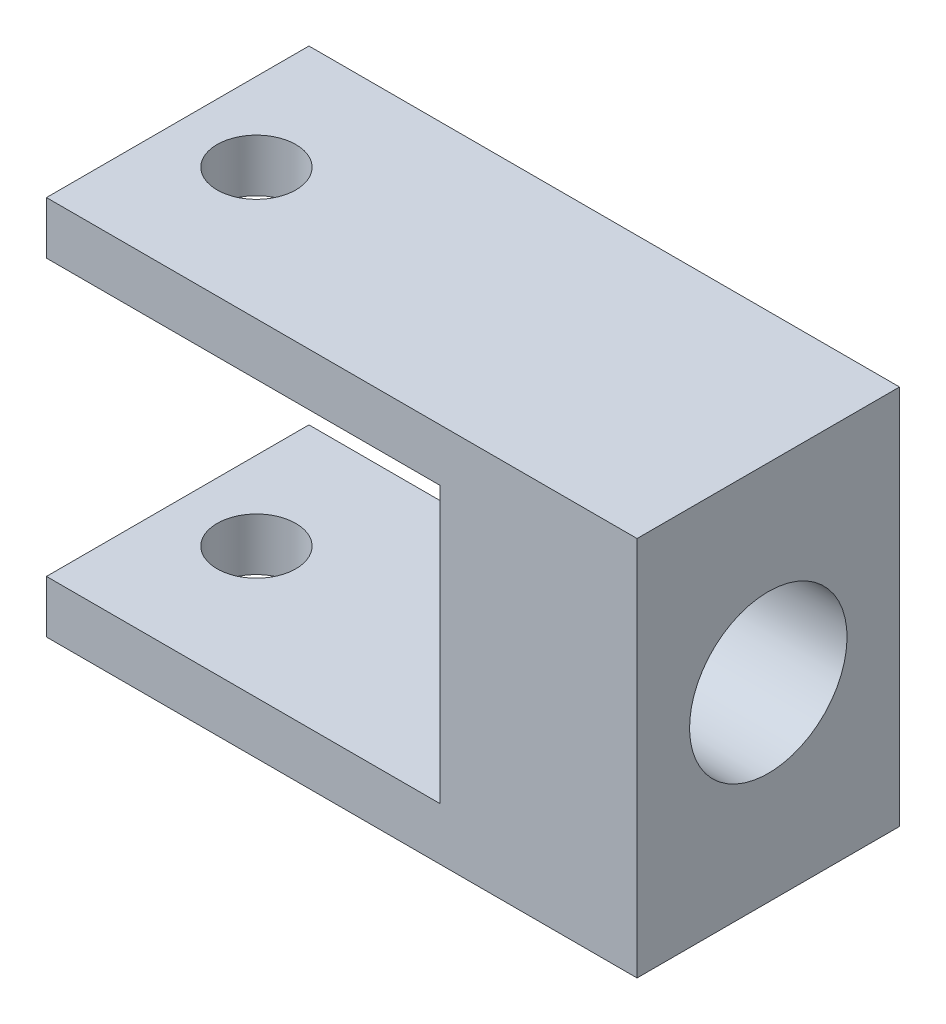
SolidWorks part; units mm, degrees
ref_plane "Ön Düzlem" through (0, 0, 0) normal (0, 0, 1) x (1, 0, 0)
ref_plane "Üst Düzlem" through (0, 0, 0) normal (0, 1, 0) x (1, 0, 0)
ref_plane "Sağ Düzlem" through (0, 0, 0) normal (1, 0, 0) x (0, 0, -1)
sketch "Çizim1" plane through (0, 0, 0) normal (0, 0, 1) x (1, 0, 0)
  line L0 (-22.5, 14.5) -> (22.5, -14.5) construction
  line L1 (-22.5, 14.5) -> (22.5, 14.5)
  line L2 (-22.5, 14.5) -> (-22.5, 10.5)
  line L3 (-22.5, -14.5) -> (22.5, -14.5)
  line L4 (22.5, 14.5) -> (22.5, -14.5)
  line L5 (-22.5, -10.5) -> (-22.5, -14.5)
  line L6 (-22.5, 10.5) -> (7.5, 10.5)
  line L8 (-22.5, -10.5) -> (7.5, -10.5)
  line L9 (7.5, 10.5) -> (7.5, -10.5)
  dimension "D1" = 29
  dimension "D2" = 45
  dimension "D3" = 4
  dimension "D4" = 4
  dimension "D5" = 30
extrude "Yükseklik-Ekstrüzyon1" add sketch "Çizim1" along normal blind 20
sketch "Çizim2" plane through (22.5, 0, 0) normal (1, 0, 0) x (0, 0, -1)
  line L0 (-20, 14.5) -> (0, -14.5) construction
  line L1 (0, 14.5) -> (-20, -14.5) construction
  circle A0 centre (-10, 0) radius 6
extrude "Kes-Ekstrüzyon1" cut sketch "Çizim2" against normal blind 20
sketch "Çizim3" plane through (0, -14.5, 0) normal (0, -1, 0) x (1, 0, 0)
  line L0 (-22.5, 20) -> (-22.5, 0) construction
  circle A0 centre (-16.5, 10) radius 3
  dimension "D1" = 6
extrude "Kes-Ekstrüzyon2" cut sketch "Çizim3" against normal blind 40
